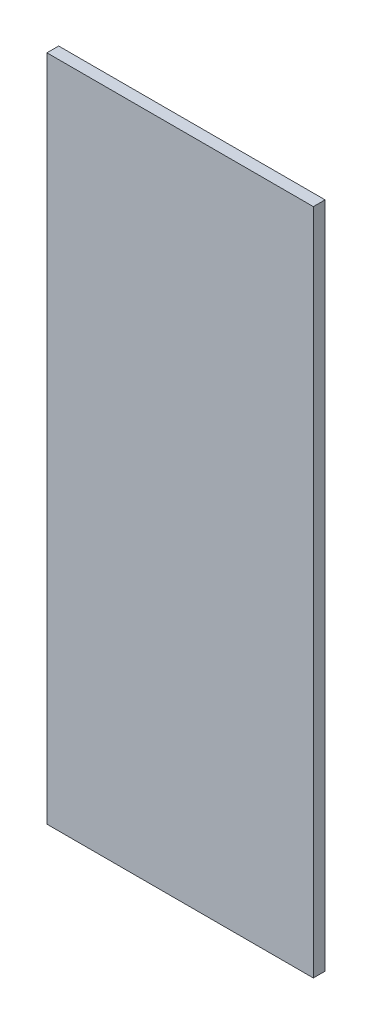
SolidWorks part; units mm, degrees
ref_plane "Front Plane" through (0, 0, 0) normal (0, 0, 1) x (1, 0, 0)
ref_plane "Top Plane" through (0, 0, 0) normal (0, 1, 0) x (1, 0, 0)
ref_plane "Right Plane" through (0, 0, 0) normal (1, 0, 0) x (0, 0, -1)
sketch "Sketch1" plane through (0, 0, 0) normal (0, 0, 1) x (1, 0, 0)
  line L1 (204, -511.5) -> (-204, -511.5)
  line L2 (204, -511.5) -> (204, 511.5)
  line L3 (204, 511.5) -> (-204, 511.5)
  line L4 (-204, -511.5) -> (-204, 511.5)
  line L5 (204, -511.5) -> (-204, 511.5) construction
  line L6 (204, 511.5) -> (-204, -511.5) construction
  point P0 (0, 0)
  dimension "D1" = 1023
  dimension "D2" = 408
extrude "Boss-Extrude1" add sketch "Sketch1" along normal blind 18
equation "\"H_DSP\"=18"
equation "\"D1@Boss-Extrude1\"=\"H_DSP\""
